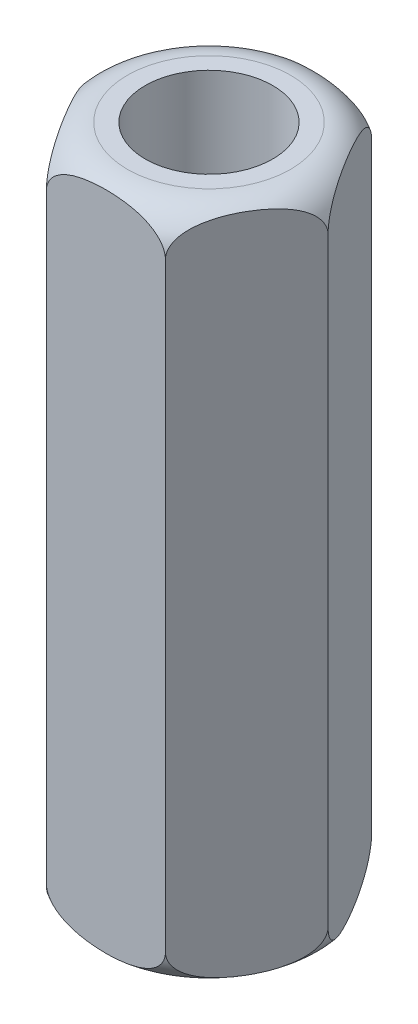
SolidWorks part; units mm, degrees
material "Brass"
ref_plane "Front Plane" through (0, 0, 0) normal (0, 0, 1) x (1, 0, 0)
ref_plane "Top Plane" through (0, 0, 0) normal (0, 1, 0) x (1, 0, 0)
ref_plane "Right Plane" through (0, 0, 0) normal (1, 0, 0) x (0, 0, -1)
sketch "Sketch1" plane through (0, 0, 0) normal (0, 1, 0) x (1, 0, 0)
  line L1 (3.1754, 0) -> (1.5877, 2.75)
  line L2 (1.5877, 2.75) -> (-1.5877, 2.75)
  line L3 (-1.5877, 2.75) -> (-3.1754, 0)
  line L4 (-3.1754, 0) -> (-1.5877, -2.75)
  line L5 (-1.5877, -2.75) -> (1.5877, -2.75)
  line L6 (1.5877, -2.75) -> (3.1754, 0)
  circle A0 centre (0, 0) radius 2.75 construction
  dimension "D1" = 5.5
extrude "Boss-Extrude1" add sketch "Sketch1" along normal blind 18
hole_wizard "M3 Clearance Hole1" positions "Sketch3" profile "Sketch2" hole size "M3" standard "ISO"
sketch "Sketch3" plane through (0, 18, 0) normal (0, 1, 0) x (-1, 0, 0)
  point P0 (0, 0)
sketch "Sketch2" plane through (0, 18, 0) normal (1, 0, 0) x (0, 0, 1)
  line L0 (0, 0) -> (0, 21.0215)
  line L1 (0, 21.0215) -> (1.7, 20)
  line L2 (1.7, 20) -> (1.7, 0)
  line L5 (1.7, 0) -> (0, 0)
  line L10 (0, 21.0215) -> (-1.7, 20) construction
  line L11 (0, -6.35) -> (0, 107.95) construction
  dimension "Hole Dia." = 3.4
  dimension "Hole Depth" = 20
  dimension "Drill Angle" = 118
sketch "Sketch4" plane through (0, 0, 0) normal (0, 0, 1) x (1, 0, 0)
  line L0 (-3.1754, 18) -> (-3.1754, 0) construction
  line L1 (-3.1754, 18) -> (-1.5877, 18) construction
  line L4 (-3.1754, 0) -> (-1.5877, 0) construction
  line L6 (-2.1754, 18) -> (-3.1754, 18)
  line L7 (-3.1754, 18) -> (-3.1754, 17)
  line L8 (-3.1754, 1) -> (-3.1754, 0)
  line L9 (-3.1754, 0) -> (-2.1754, 0)
  line L14 (0, 18) -> (0, 0) construction
  line L15 (-1.5877, 18) -> (1.5877, 18) construction
  arc A0 (-3.1754, 17) -> (-2.1754, 18) centre (-2.1754, 17) cw
  arc A2 (-3.1754, 1) -> (-2.1754, 0) centre (-2.1754, 1) ccw
  dimension "D1" = 1
revolve "Cut-Revolve1" cut sketch "Sketch4" angle 360 about L14
